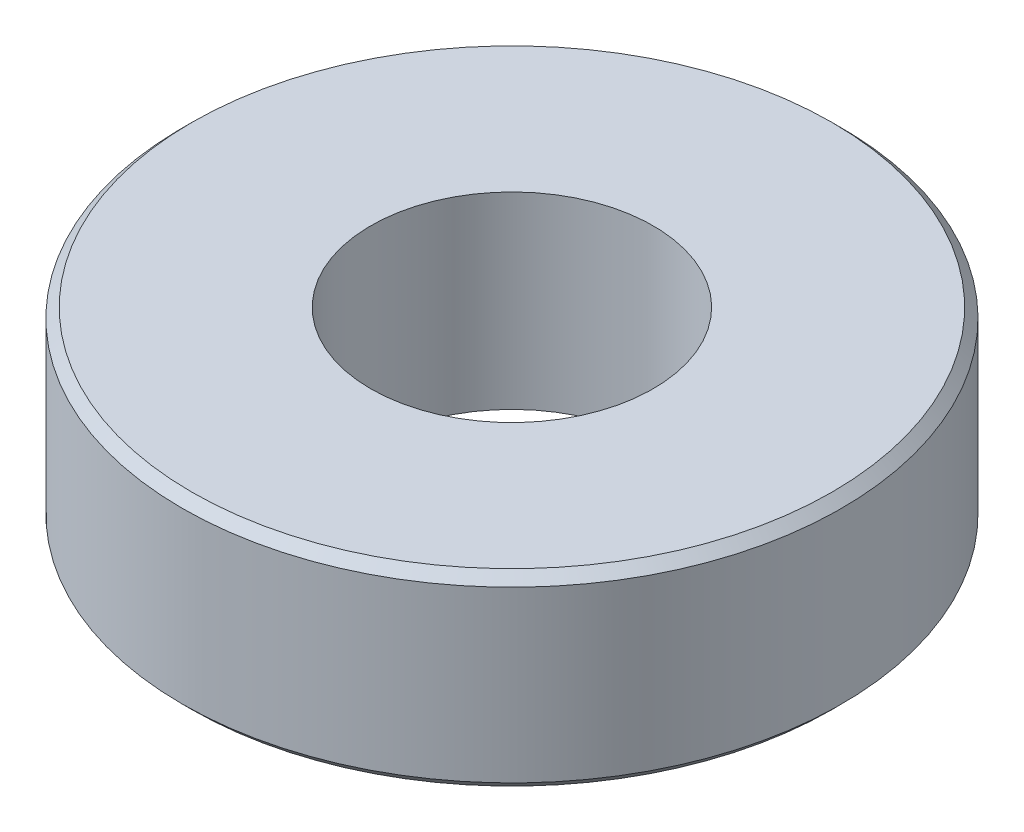
SolidWorks part; units mm, degrees
material "AISI 316 退火不锈钢条 (SS)"
ref_plane "前视基准面" through (0, 0, 0) normal (0, 0, 1) x (1, 0, 0)
ref_plane "上视基准面" through (0, 0, 0) normal (0, 1, 0) x (1, 0, 0)
ref_plane "右视基准面" through (0, 0, 0) normal (1, 0, 0) x (0, 0, -1)
sketch "草图1" plane through (0, 0, 0) normal (0, 1, 0) x (1, 0, 0)
  circle A0 centre (0, 0) radius 3
  circle A1 centre (0, 0) radius 7
  dimension "D1" = 6
  dimension "D2" = 14
extrude "凸台-拉伸1" add sketch "草图1" along normal blind 4
chamfer "倒角1" distance 0.2 angle 45 2 edges at (0, 0, 7) (0, 4, 7)
